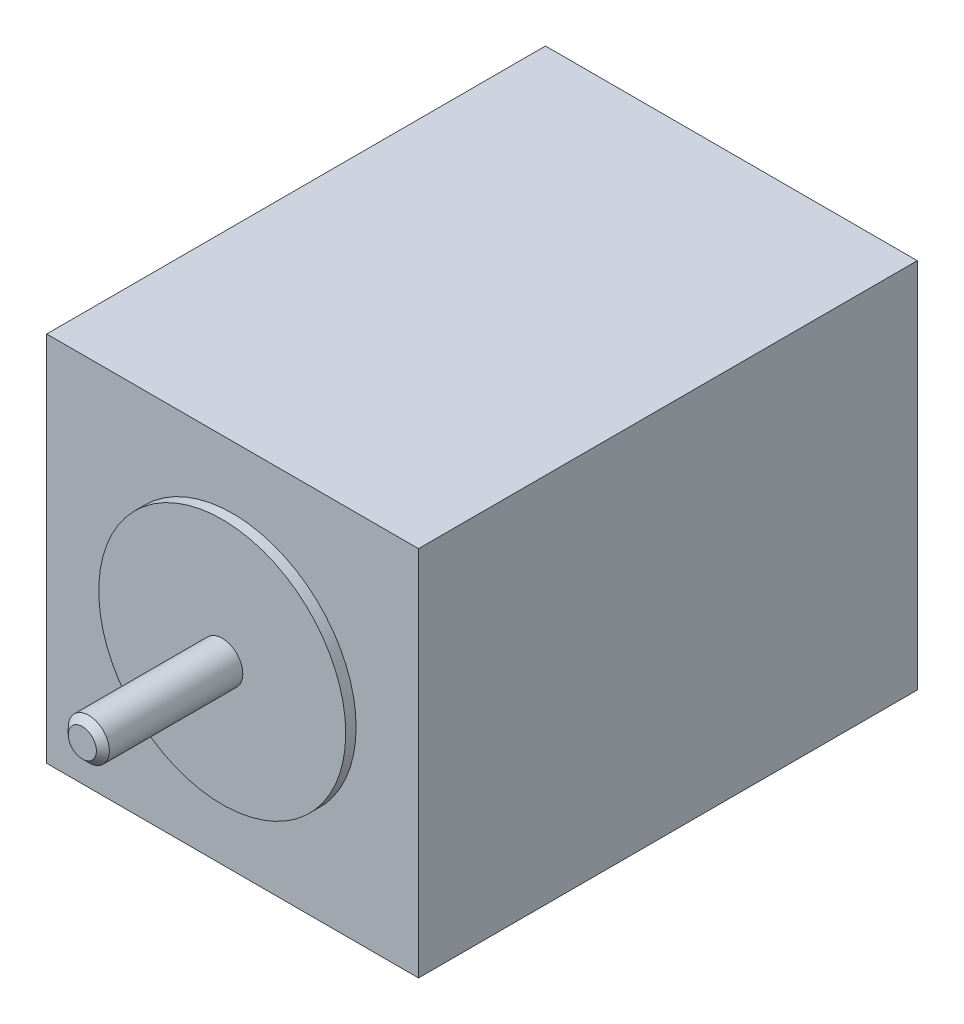
SolidWorks part; units mm, degrees
ref_plane "Ebene vorne" through (0, 0, 0) normal (0, 0, 1) x (1, 0, 0)
ref_plane "Ebene oben" through (0, 0, 0) normal (0, 1, 0) x (1, 0, 0)
ref_plane "Ebene rechts" through (0, 0, 0) normal (1, 0, 0) x (0, 0, -1)
sketch "Skizze1" plane through (0, 0, 0) normal (0, 0, 1) x (1, 0, 0)
  line L0 (0, 0) -> (57.4, 0)
  line L1 (57.4, 0) -> (57.4, 57.4)
  line L2 (57.4, 57.4) -> (0, 57.4)
  line L3 (0, 57.4) -> (0, 0)
  dimension "D1" = 57.4
  dimension "D2" = 57.4
extrude "Aufsatz-Linear austragen1" add sketch "Skizze1" against normal blind 77
sketch "Skizze2" plane through (0, 0, 0) normal (0, 0, 1) x (1, 0, 0)
  line L0 (57.4, 57.4) -> (0, 57.4) construction
  line L2 (0, 57.4) -> (0, 0) construction
  circle A0 centre (28.7, 28.7) radius 19.065
  dimension "D1" = 38.13
  dimension "D2" = 28.7
  dimension "D3" = 28.7
extrude "Aufsatz-Linear austragen2" add sketch "Skizze2" along normal blind 1.6
sketch "Skizze3" plane through (0, 0, 1.6) normal (0, 0, 1) x (1, 0, 0)
  line L0 (57.4, 57.4) -> (0, 57.4) construction
  line L2 (0, 57.4) -> (0, 0) construction
  circle A0 centre (28.7, 28.7) radius 3.175
  point P6 (0, 0)
  dimension "D3" = 6.35
  dimension "D1" = 28.7
  dimension "D2" = 28.7
extrude "Aufsatz-Linear austragen3" add sketch "Skizze3" along normal blind 21.6
chamfer "Fase1" distance 1 angle 45 1 edges at (31.875, 28.7, 23.2)
